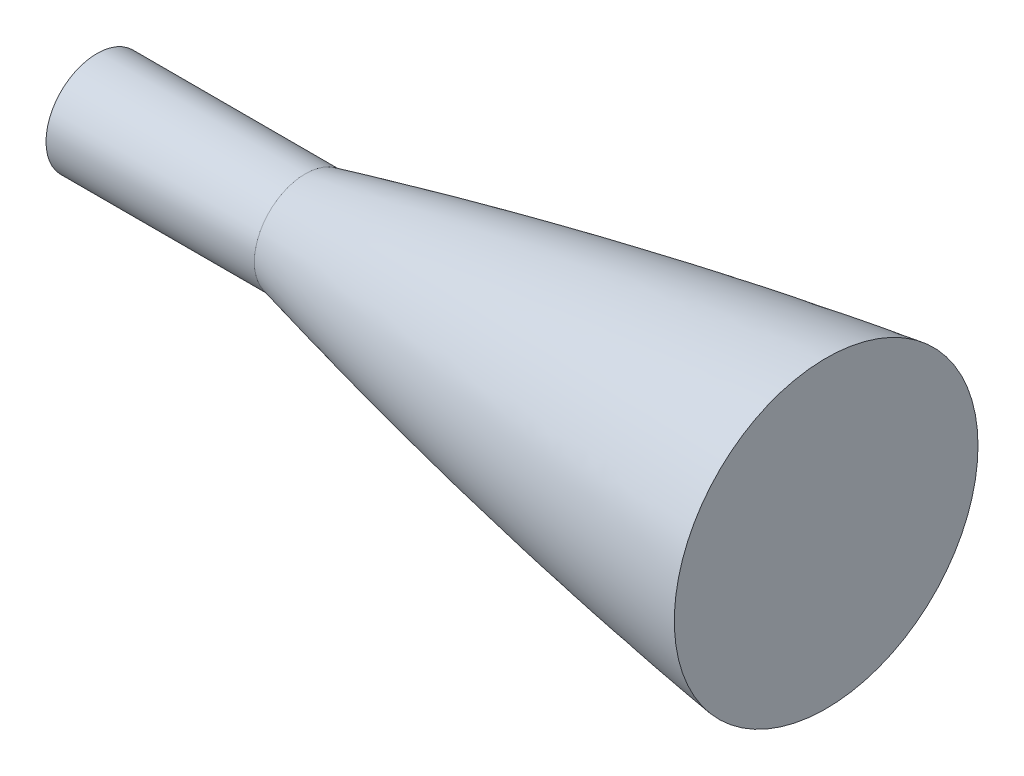
SolidWorks part; units mm, degrees
ref_plane "Front Plane" through (0, 0, 0) normal (0, 0, 1) x (1, 0, 0)
ref_plane "Top Plane" through (0, 0, 0) normal (0, 1, 0) x (1, 0, 0)
ref_plane "Right Plane" through (0, 0, 0) normal (1, 0, 0) x (0, 0, -1)
sketch "Sketch1" plane through (0, 0, 0) normal (0, 1, 0) x (1, 0, 0)
  line L0 (355.6, 50.8) -> (355.6, 1.27)
  line L1 (355.6, 1.27) -> (50.8, 1.27)
  line L2 (50.8, 13.6816) -> (50.8, 1.27)
  spline S0 degree 4 poles (21.2341, 5.9936) (21.856, 6.1634) (23.0998, 6.5019) (25.5843, 7.1746) (28.69, 8.0062) (31.7724, 8.8231) (34.8672, 9.6339) (37.2923, 10.2647) (39.7915, 10.9085) (42.145, 11.5111) (44.7925, 12.1812) (46.8566, 12.7019) (49.9381, 13.4687) (51.3469, 13.8173) (53.9013, 14.445) (55.9043, 14.9331) (57.9182, 15.4203) (59.9692, 15.9131) (62.0056, 16.3987) (64.0459, 16.8817) (66.6196, 17.4865) (69.7274, 18.2096) (73.3707, 19.0464) (77.5504, 19.9917) (82.7791, 21.1557) (97.434, 24.3488) (119.4856, 28.817) (168.0008, 37.516) (219.035, 44.0813) (262.8224, 47.8202) (299.2065, 49.5707) (308.8412, 49.9474) (315.2656, 50.1624) (319.549, 50.2912) (323.8328, 50.4056) (328.117, 50.5056) (332.4014, 50.5911) (336.1391, 50.6531) (339.3296, 50.6971) (341.9732, 50.7276) (344.0698, 50.7484) (346.1633, 50.7657) (348.2725, 50.7795) (350.3447, 50.7899) (352.4057, 50.7968) (355.0352, 50.8005) (356.4848, 50.8002) (359.6537, 50.7954) (361.7791, 50.7854) (364.5032, 50.7703) (366.9275, 50.7502) (369.503, 50.7251) (372.0018, 50.695) (374.5511, 50.6597) (377.0919, 50.6192) (379.6547, 50.5733) (382.2234, 50.522) (384.1523, 50.4796) (385.4374, 50.4496) (386.0799, 50.4342) knots 0 0 0 0 0 0.006986 0.013973 0.027946 0.034806 0.041666 0.048526 0.055386 0.062246 0.069106 0.075966 0.082827 0.088511 0.094195 0.099879 0.105563 0.111247 0.116931 0.122615 0.128299 0.139917 0.151536 0.163154 0.174773 0.19801 0.314194 0.407142 0.709223 0.755697 0.790552 0.802171 0.813789 0.825408 0.837026 0.848645 0.860263 0.871882 0.877566 0.88325 0.888934 0.894618 0.900302 0.905986 0.91167 0.917354 0.924199 0.931044 0.937889 0.944735 0.95158 0.958425 0.96527 0.972115 0.979087 0.986058 0.993029 1 1 1 1 1 construction
  spline S1 degree 4 poles (50.8, 13.6816) (51.2246, 13.7865) (52.0797, 13.9974) (53.9013, 14.445) (55.9043, 14.9331) (57.9182, 15.4203) (59.9692, 15.9131) (62.0056, 16.3987) (64.0459, 16.8817) (66.6196, 17.4865) (69.7274, 18.2096) (73.3707, 19.0464) (77.5504, 19.9917) (82.7791, 21.1557) (97.434, 24.3488) (119.4856, 28.817) (168.0008, 37.516) (219.035, 44.0813) (262.8224, 47.8202) (299.2065, 49.5707) (308.8412, 49.9474) (315.2656, 50.1624) (319.549, 50.2912) (323.8328, 50.4056) (328.117, 50.5056) (332.4014, 50.5911) (336.1391, 50.6531) (339.3296, 50.6971) (341.9732, 50.7276) (344.0698, 50.7484) (346.1633, 50.7657) (348.2725, 50.7795) (350.3447, 50.7899) (352.4057, 50.7968) (354.282, 50.7994) (355.1626, 50.8) (355.6, 50.8) knots 0.082827 0.082827 0.082827 0.082827 0.082827 0.088511 0.094195 0.099879 0.105563 0.111247 0.116931 0.122615 0.128299 0.139917 0.151536 0.163154 0.174773 0.19801 0.314194 0.407142 0.709223 0.755697 0.790552 0.802171 0.813789 0.825408 0.837026 0.848645 0.860263 0.871882 0.877566 0.88325 0.888934 0.894618 0.900302 0.905986 0.91167 0.917354 0.917354 0.917354 0.917354 0.917354
  dimension "D1" = 49.53
  dimension "D2" = 12.4116
revolve "Revolve2" add sketch "Sketch1" angle 360 about L1
ref_plane "Plane1" through (358.14, 0, 0) normal (1, 0, 0) x (0, 0, -1)
sketch "Sketch2" plane through (355.6, 0, 0) normal (1, 0, 0) x (0, 0, -1)
  line L1 (-48.26, 0) -> (50.8, 0) construction
  circle A0 centre (1.27, 0) radius 49.53 construction
  circle A1 centre (1.27, 0) radius 49.53
extrude "Boss-Extrude1" add sketch "Sketch2" along normal blind 203.2
sketch "Sketch3" plane through (50.8, 0, 0) normal (-1, 0, 0) x (0, 0, 1)
  line L0 (-13.6816, 0) -> (11.1416, 0) construction
  circle A0 centre (-1.27, 0) radius 12.4116 construction
  circle A1 centre (-1.27, 0) radius 12.4116
extrude "Boss-Extrude2" add sketch "Sketch3" along normal blind 50.8
ref_plane "Plane2" through (368.3, 0, 0) normal (1, 0, 0) x (0, 0, -1)
sketch "Sketch4" plane through (368.3, 0, 0) normal (1, 0, 0) x (0, 0, -1)
  line L0 (-48.26, 0) -> (50.8, 0) construction
  circle A0 centre (1.27, 0) radius 49.53 construction
  circle A1 centre (1.27, 0) radius 49.53
extrude "Cut-Extrude1" cut sketch "Sketch4" along normal blind 381
ref_plane "Plane3" through (177.8, 0, 0) normal (1, 0, 0) x (0, 0, -1)
sketch "Sketch5" plane through (177.8, 0, 0) normal (1, 0, 0) x (0, 0, -1)
  circle A0 centre (1.27, 0) radius 49.53
extrude "Cut-Extrude2" cut sketch "Sketch5" along normal blind 381
